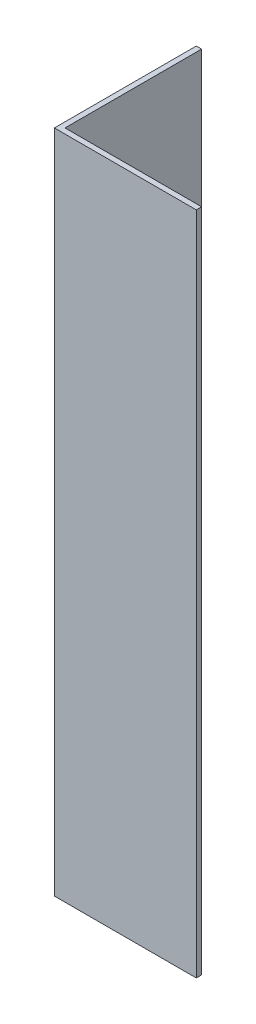
SolidWorks part; units mm, degrees
material "1060 Сплав"
ref_plane "Спереди" through (0, 0, 0) normal (0, 0, 1) x (1, 0, 0)
ref_plane "Сверху" through (0, 0, 0) normal (0, 1, 0) x (1, 0, 0)
ref_plane "Справа" through (0, 0, 0) normal (1, 0, 0) x (0, 0, -1)
sketch "Эскиз1" plane through (0, 0, 0) normal (0, 1, 0) x (1, 0, 0)
  line L0 (0, 0) -> (0, 20)
  line L1 (0, 20) -> (0.75, 20)
  line L2 (0.75, 20) -> (0.75, 0.75)
  line L3 (0.75, 0.75) -> (20, 0.75)
  line L4 (20, 0.75) -> (20, 0)
  line L5 (20, 0) -> (0, 0)
  dimension "D1" = 0.75
  dimension "D2" = 20
extrude "Бобышка-Вытянуть1" add sketch "Эскиз1" along normal blind 93.75
